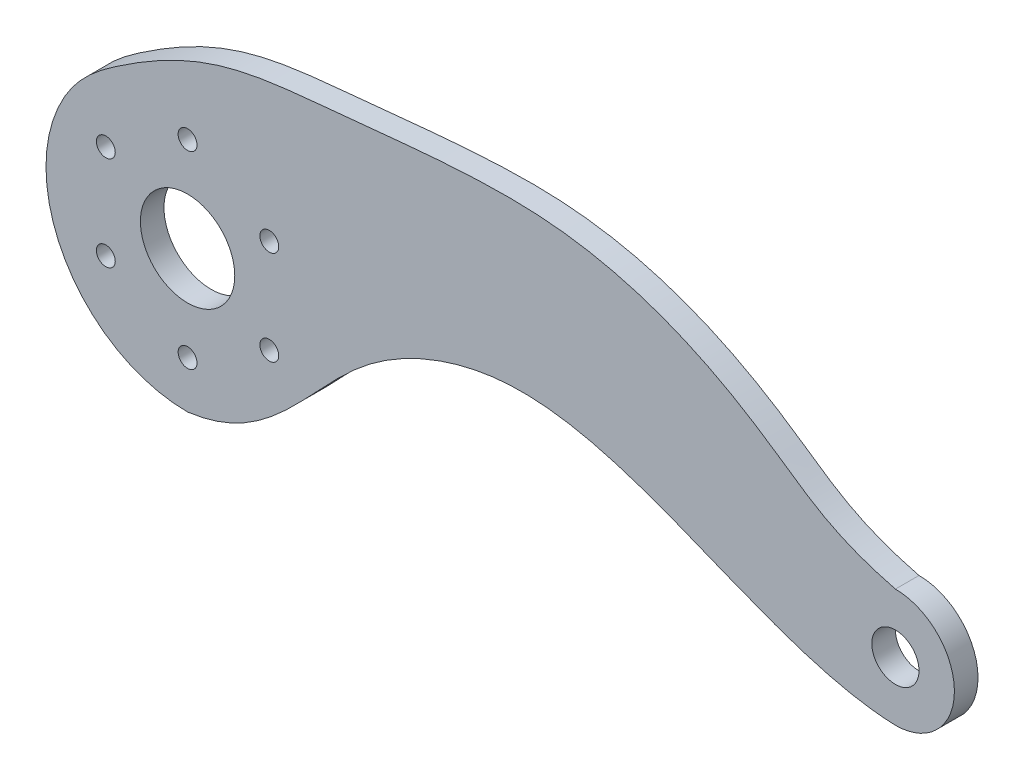
SolidWorks part; units mm, degrees
material "6063-T6"
ref_plane "Front Plane" through (0, 0, 0) normal (0, 0, 1) x (1, 0, 0)
ref_plane "Top Plane" through (0, 0, 0) normal (0, 1, 0) x (1, 0, 0)
ref_plane "Right Plane" through (0, 0, 0) normal (1, 0, 0) x (0, 0, -1)
sketch "Sketch1" plane through (0, 0, 0) normal (0, 0, 1) x (1, 0, 0)
  line L0 (150, 0) -> (0, 0) construction
  line L3 (0, 0) -> (-30, 0) construction
  line L4 (0, 0) -> (0, -30) construction
  arc A8 (0, 30) -> (0, -30) centre (0, 0) ccw
  circle A9 centre (0, 0) radius 20
  circle A18 centre (0, 20) radius 2
  circle A25 centre (0, 0) radius 10
  arc A27 (150, -12.5) -> (150, 12.5) centre (150, 0) ccw
  circle A28 centre (150, 0) radius 5
  circle A29 centre (17.3205, 10) radius 2
  circle A30 centre (17.3205, -10) radius 2
  circle A31 centre (0, -20) radius 2
  circle A32 centre (-17.3205, -10) radius 2
  circle A33 centre (-17.3205, 10) radius 2
  spline S0 degree 2 poles (150, -12.5) (154.8811, -13.0472) (159.4285, -8.207) knots 0.955766 0.955766 0.955766 1 1 1
  spline S1 degree 3 poles (0, -30) (17.9368, -27.7459) (30.1702, -2.352) (85.2159, 19.612) (122.1994, -11.5342) (150, -12.5) knots 0 0 0 0 0.288189 0.47594 1 1 1 1
  spline S2 degree 3 poles (-26.0635, 14.8558) (-22.9952, 20.2389) (2.3733, 39.108) (20.1598, 39.1077) (86.7416, 46.9998) (125.8129, 25.8301) (135.8827, 16.0755) (150, 12.5) knots 0 0 0 0 0.056044 0.324797 0.474988 0.725167 0.945335 0.945335 0.945335 0.945335
  spline S3 degree 2 poles (158.705, 8.9707) (159.0865, 8.6177) (159.4285, 8.207) knots 0.994494 0.994494 0.994494 1 1 1
  point P36 (0, 0)
  dimension "D2" = 4
  dimension "D3" = 20
  dimension "D4" = 40
  dimension "D6" = 30
  dimension "D7" = 10
  dimension "D8" = 6
  dimension "D5" = 25
  dimension "D11" = 150
extrude "Boss-Extrude3" add sketch "Sketch1" along normal blind 5
